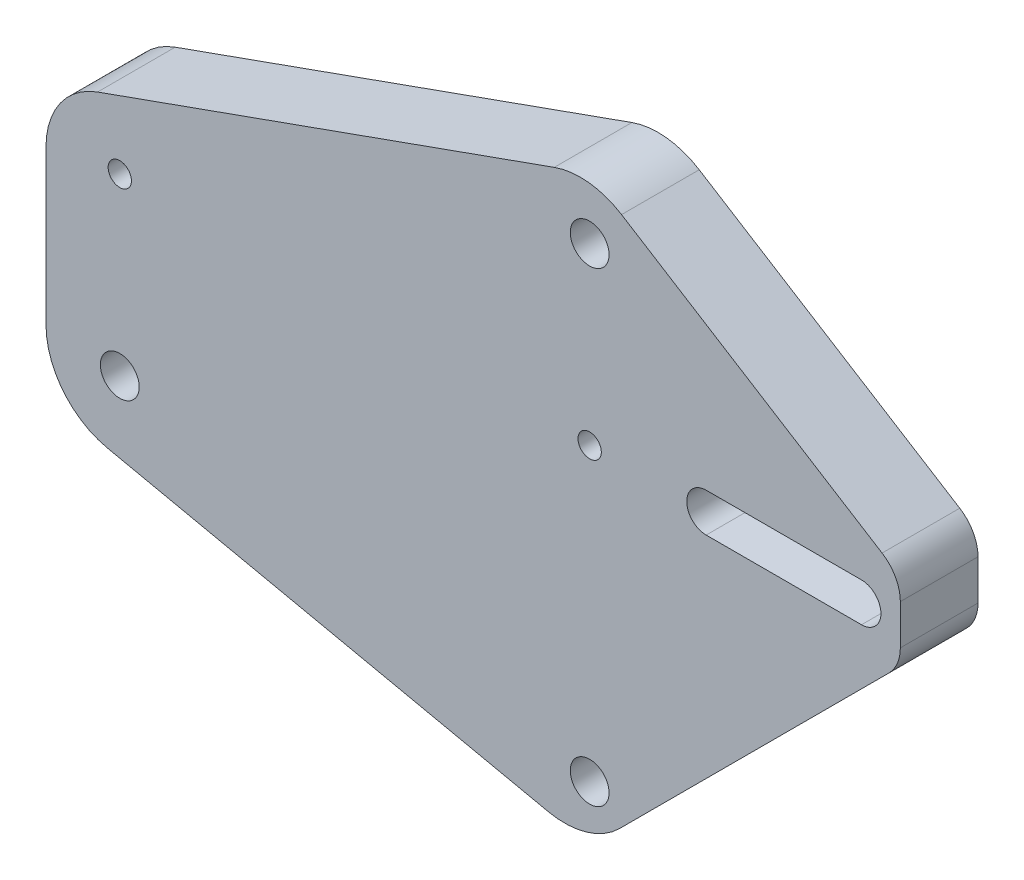
SolidWorks part; units mm, degrees
ref_plane "Front Plane" through (0, 0, 0) normal (0, 0, 1) x (1, 0, 0)
ref_plane "Top Plane" through (0, 0, 0) normal (0, 1, 0) x (1, 0, 0)
ref_plane "Right Plane" through (0, 0, 0) normal (1, 0, 0) x (0, 0, -1)
sketch "Sketch1" plane through (0, 0, 0) normal (0, 0, 1) x (1, 0, 0)
  line L1 (-44.5586, 33.3719) -> (-103.3634, 12.3702)
  line L2 (-110, 2.9528) -> (-110, -16.9158)
  line L3 (-102.0953, -26.6939) -> (-45.3195, -38.8601)
  line L4 (-36.1531, -36.1531) -> (-1.4645, -1.4645)
  line L5 (-35.8952, 32.4345) -> (-2.35, 11.4688)
  line L6 (0, 7.2288) -> (0, 2.0711)
  line L7 (-25, 4.6499) -> (-5, 4.6499) construction
  line L8 (-25, 7.1499) -> (-5, 7.1499)
  line L9 (-25, 2.1499) -> (-5, 2.1499)
  circle A0 centre (-40, 4.6499) radius 1.5
  arc A1 (-25, 7.1499) -> (-25, 2.1499) centre (-25, 4.6499) ccw
  arc A2 (-5, 2.1499) -> (-5, 7.1499) centre (-5, 4.6499) ccw
  circle A3 centre (-40, 27.1499) radius 2.5
  circle A4 centre (-100.5, 4.6499) radius 1.5
  circle A5 centre (-100.5, -17.8501) radius 2.5
  circle A6 centre (-40, -32.8501) radius 2.5
  arc A7 (-35.8952, 32.4345) -> (-44.5586, 33.3719) centre (-41.1952, 23.9545) ccw
  arc A8 (-45.3195, -38.8601) -> (-36.1531, -36.1531) centre (-43.2242, -29.0821) ccw
  arc A9 (-110, -16.9158) -> (-102.0953, -26.6939) centre (-100, -16.9158) ccw
  arc A10 (-103.3634, 12.3702) -> (-110, 2.9528) centre (-100, 2.9528) ccw
  arc A11 (0, 2.0711) -> (-1.4645, -1.4645) centre (-5, 2.0711) cw
  arc A12 (-2.35, 11.4688) -> (0, 7.2288) centre (-5, 7.2288) cw
  point P9 (0, 4.6499)
  point P11 (-15, 4.6499)
  point P44 (-40, 35)
  point P47 (-40, -40)
  point P50 (-110, -25)
  point P53 (-110, 10)
  point P56 (0, 0)
  point P59 (0, 10)
  dimension "D1" = 3
  dimension "D8" = 2.5
  dimension "D9" = 20
  dimension "D10" = 5
  dimension "D12" = 3
  dimension "D14" = 5
  dimension "D17" = 5
  dimension "D22" = 10
  dimension "D23" = 5
  dimension "D2" = 35
  dimension "D3" = 70
  dimension "D4" = 10
  dimension "D5" = 40
  dimension "D6" = 40
  dimension "D7" = 40
  dimension "D11" = 22.5
  dimension "D13" = 60.5
  dimension "D15" = 22.5
  dimension "D16" = 60
  dimension "D18" = 15
  dimension "D19" = 25
  dimension "D20" = 40
  dimension "D21" = 15
extrude "Boss-Extrude2" add sketch "Sketch1" along normal blind 10
